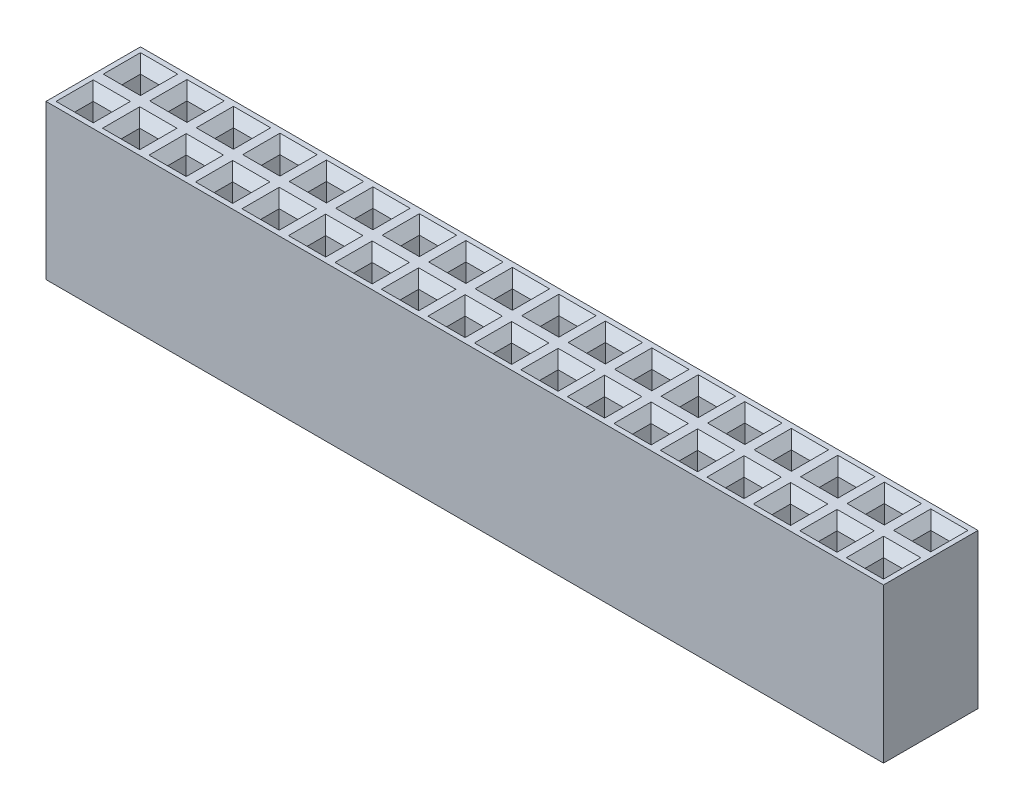
SolidWorks part; units mm, degrees
ref_plane "Front Plane" through (0, 0, 0) normal (0, 0, 1) x (1, 0, 0)
ref_plane "Top Plane" through (0, 0, 0) normal (0, 1, 0) x (1, 0, 0)
ref_plane "Right Plane" through (0, 0, 0) normal (1, 0, 0) x (0, 0, -1)
sketch "Sketch1" plane through (0, 0, 0) normal (0, 1, 0) x (1, 0, 0)
  line L0 (1.27, -1.27) -> (1.27, 1.27)
  line L1 (1.27, -1.27) -> (-1.27, -1.27)
  line L2 (1.27, 1.27) -> (-1.27, 1.27)
  line L3 (-1.27, -1.27) -> (-1.27, 1.27)
  line L4 (1.27, -1.27) -> (-1.27, 1.27) construction
  line L5 (1.27, 1.27) -> (-1.27, -1.27) construction
  point P1 (0, 0)
  dimension "D1" = 2.54
  dimension "D2" = 2.54
extrude "Boss-Extrude1" add sketch "Sketch1" along normal blind 8.3
sketch "Sketch2" plane through (0, 8.3, 0) normal (0, 1, 0) x (-1, 0, 0)
  line L0 (-0.5, 0.5) -> (-0.5, -0.5)
  line L1 (-0.5, 0.5) -> (0.5, 0.5)
  line L2 (-0.5, -0.5) -> (0.5, -0.5)
  line L3 (0.5, 0.5) -> (0.5, -0.5)
  line L4 (-0.5, 0.5) -> (0.5, -0.5) construction
  line L5 (-0.5, -0.5) -> (0.5, 0.5) construction
  point P1 (0, 0)
  dimension "D1" = 1
  dimension "D2" = 1
extrude "Cut-Extrude1" cut sketch "Sketch2" against normal blind 4
chamfer "Chamfer1" distance 0.5 angle 45 4 edges at (0, 8.3, 0.5) (0.5, 8.3, 0) (0, 8.3, -0.5) (-0.5, 8.3, 0)
pattern_linear "LPattern1" count 18 spacing 2.5 along (1, 0, 0) count 2 spacing 2.54 along (0, 0, -1) of "Boss-Extrude1", "Cut-Extrude1", "Chamfer1"
